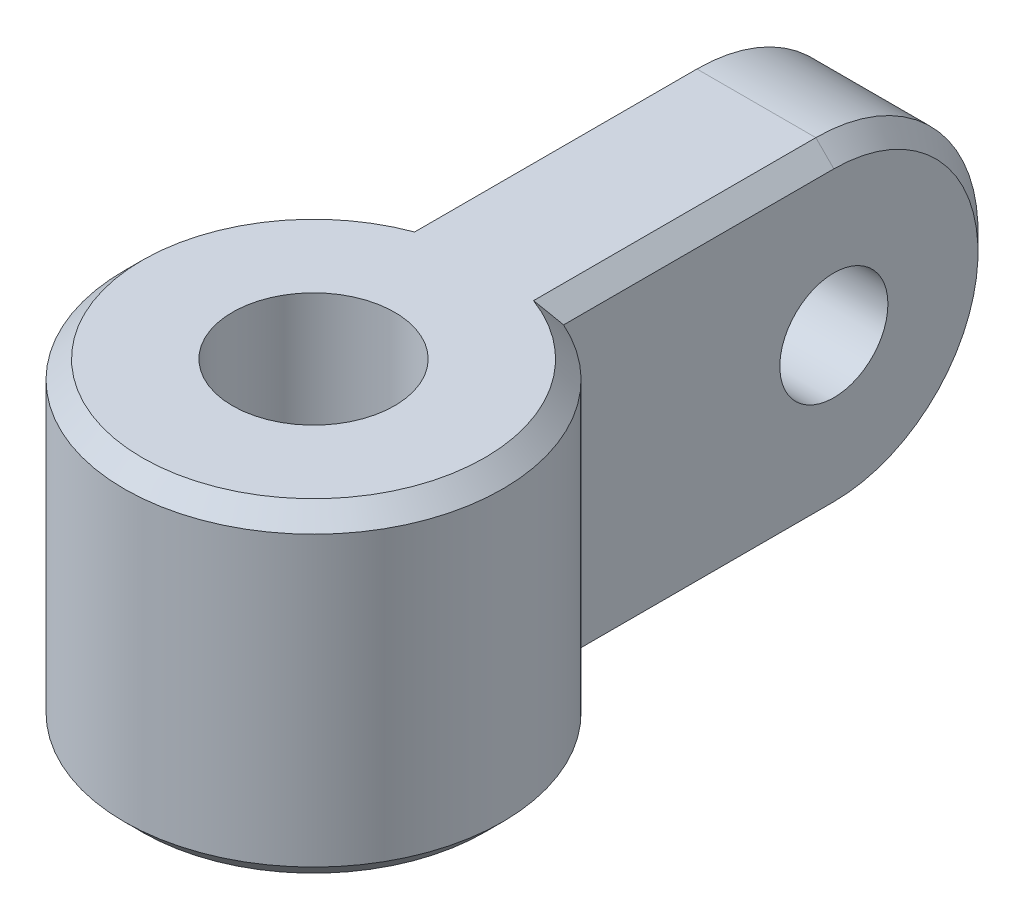
SolidWorks part; units mm, degrees
ref_plane "Front Plane" through (0, 0, 0) normal (0, 0, 1) x (1, 0, 0)
ref_plane "Top Plane" through (0, 0, 0) normal (0, 1, 0) x (1, 0, 0)
ref_plane "Right Plane" through (0, 0, 0) normal (1, 0, 0) x (0, 0, -1)
sketch "Sketch1" plane through (0, 0, 0) normal (0, 1, 0) x (1, 0, 0)
  line L5 (-2.15, 4.7896) -> (2.15, 4.7896)
  line L6 (-2.15, 4.7896) -> (-2.15, 7.7896)
  line L7 (-2.15, 7.7896) -> (2.15, 7.7896)
  line L8 (2.15, 4.7896) -> (2.15, 7.7896)
  circle A0 centre (0, 0) radius 2.25
  arc A2 (-2.15, 4.7896) -> (2.15, 4.7896) centre (0, 0) ccw
  point P5 (0, 0)
  point P6 (0, 0)
  dimension "D1" = 4.5
  dimension "D3" = 3
  dimension "D2" = 4.3
  dimension "D4" = 3
extrude "Boss-Extrude1" add sketch "Sketch1" along normal blind 9 contours L5 A2 A0 | L5 L8 L7 L6
sketch "Sketch3" plane through (2.15, 0, 0) normal (1, 0, 0) x (0, 0, -1)
  line L0 (7.7896, 4.5) -> (12.2896, 4.5) construction
  line L1 (12.2896, 4.5) -> (16.7896, 4.5) construction
  line L2 (12.2896, 0) -> (7.7896, 0)
  line L3 (7.7896, 9) -> (12.2896, 9)
  line L4 (4.7896, 0) -> (7.7896, 0)
  line L5 (7.7896, 0) -> (7.7896, 9)
  line L6 (7.7896, 9) -> (4.7896, 9)
  line L7 (4.7896, 9) -> (4.7896, 0)
  line L8 (4.7896, 0) -> (7.7896, 0)
  line L9 (7.7896, 0) -> (7.7896, 9)
  line L10 (7.7896, 9) -> (4.7896, 9)
  line L11 (4.7896, 9) -> (4.7896, 0)
  arc A0 (12.2896, 9) -> (12.2896, 0) centre (12.2896, 4.5) cw
  circle A1 centre (12.2896, 4.5) radius 1.5
  line M9 (7.7896, 0) -> (7.7896, 9)
  dimension "D2" = 3
  dimension "D1" = 0
extrude "Boss-Extrude2" add sketch "Sketch3" against normal up to surface (4.3 mm away) contours A0 L3 L2 A1 M9 up to face at (-2.15, 4.5, -6.2896)
chamfer "Chamfer1" distance 0.5 angle 45 8 edges at (0, 0, 5.25) (-2.15, 0, -8.5396) (2.15, 0, -8.5396) (-2.15, 4.5, -16.7896) (2.15, 4.5, -16.7896) (-2.15, 9, -8.5396) (2.15, 9, -8.5396) (0, 9, 5.25)
